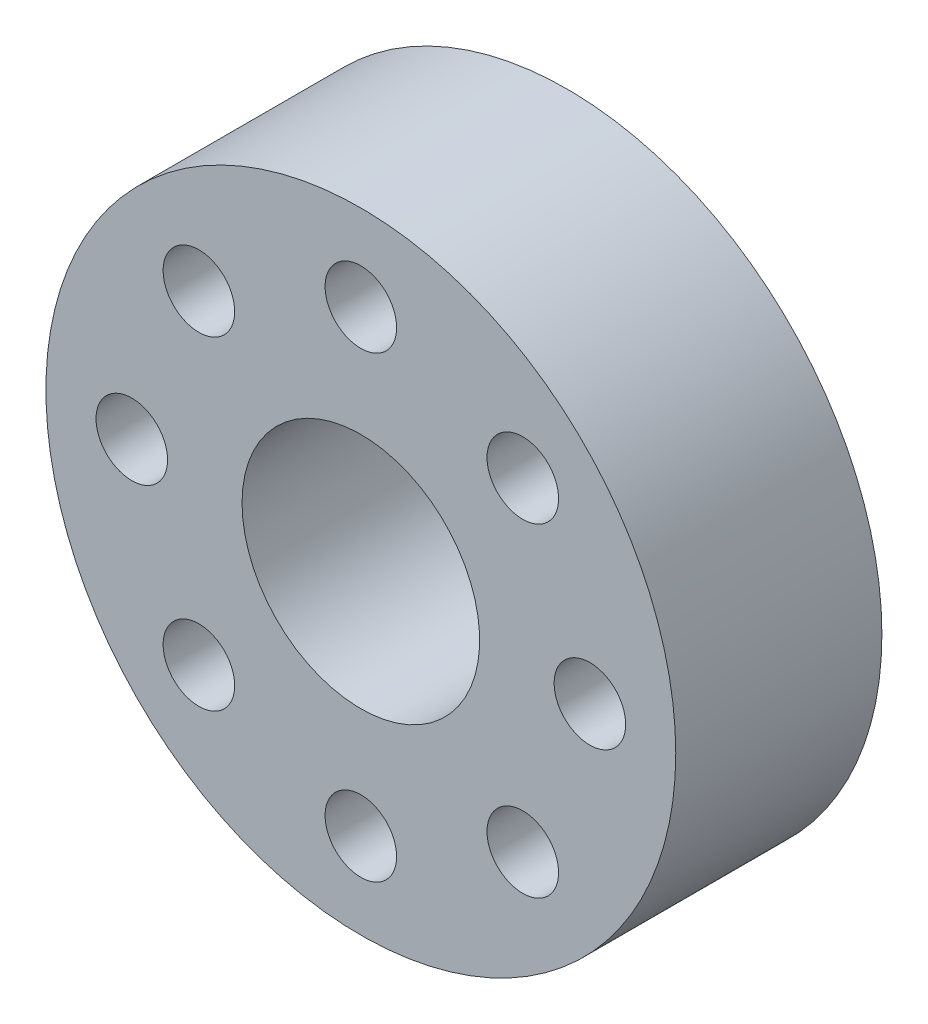
SolidWorks part; units mm, degrees
ref_plane "Front Plane" through (0, 0, 0) normal (0, 0, 1) x (1, 0, 0)
ref_plane "Top Plane" through (0, 0, 0) normal (0, 1, 0) x (1, 0, 0)
ref_plane "Right Plane" through (0, 0, 0) normal (1, 0, 0) x (0, 0, -1)
sketch "Sketch2" plane through (0, 0, 0) normal (0, 0, 1) x (1, 0, 0)
  circle A0 centre (0, 0) radius 11
  dimension "D1" = 22
extrude "Boss-Extrude1" add sketch "Sketch2" along normal blind 7.2
sketch "Sketch3" plane through (0, 0, 0) normal (0, 0, -1) x (-1, 0, 0)
  circle A0 centre (0, 0) radius 4.15
  circle A1 centre (8, 0) radius 1.25
  circle A2 centre (5.6569, -5.6569) radius 1.25
  circle A3 centre (0, -8) radius 1.25
  circle A4 centre (-5.6569, -5.6569) radius 1.25
  circle A5 centre (-8, 0) radius 1.25
  circle A6 centre (-5.6569, 5.6569) radius 1.25
  circle A7 centre (0, 8) radius 1.25
  circle A8 centre (5.6569, 5.6569) radius 1.25
  point P22 (0, 0)
  dimension "D1" = 8.3
  dimension "D3" = 2.5
  dimension "D2" = 8
  dimension "D4" = 8
extrude "Cut-Extrude1" cut sketch "Sketch3" against normal through all
